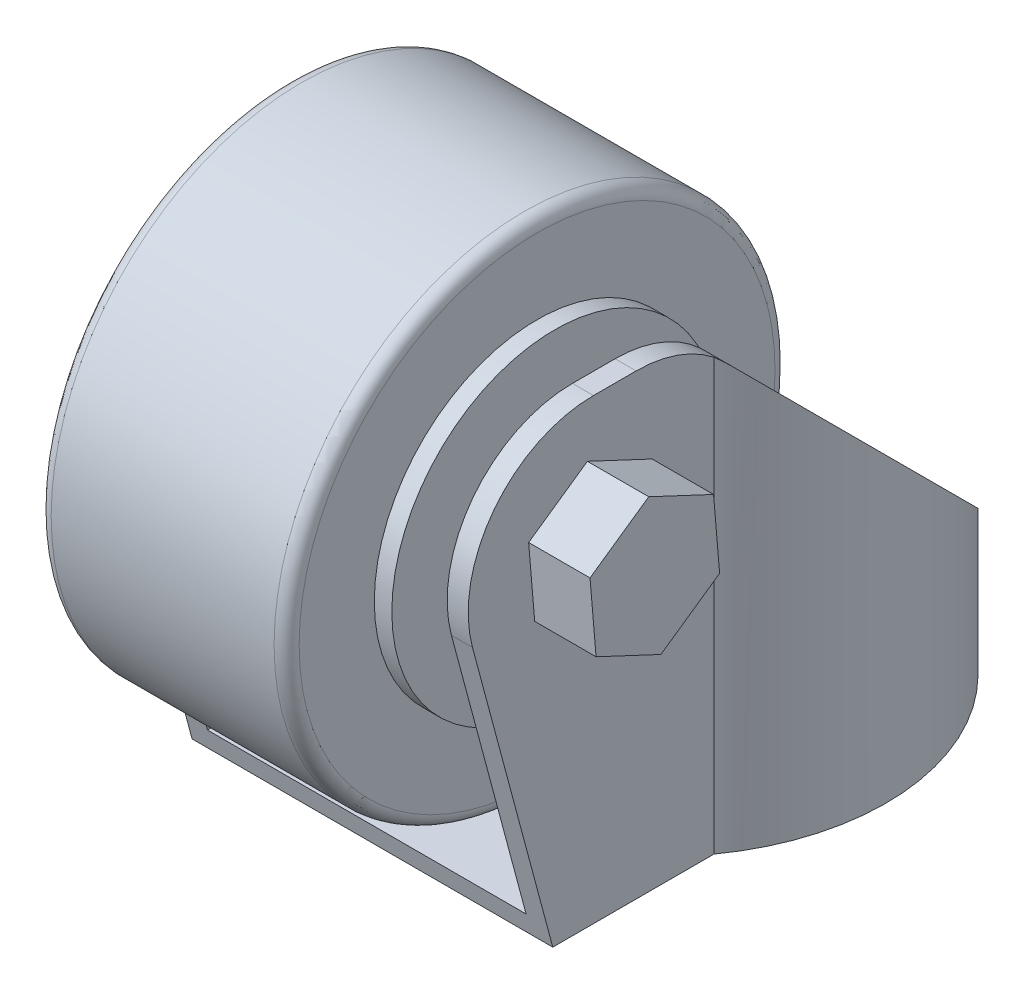
SolidWorks part; units mm, degrees
ref_plane "前视基准面" through (0, 0, 0) normal (0, 0, 1) x (1, 0, 0)
ref_plane "上视基准面" through (0, 0, 0) normal (0, 1, 0) x (1, 0, 0)
ref_plane "右视基准面" through (0, 0, 0) normal (1, 0, 0) x (0, 0, -1)
sketch "草图1" plane through (0, 0, 0) normal (0, 1, 0) x (1, 0, 0)
  line L0 (0, 0) -> (0, 47.6853) construction
  line L1 (-15.1, -30) -> (15.1, -30)
  line L2 (-21.5, -23.6) -> (-21.5, 23.6)
  line L3 (-15.1, 30) -> (15.1, 30)
  line L4 (21.5, -23.6) -> (21.5, 23.6)
  line L5 (-21.5, -30) -> (21.5, 30) construction
  line L6 (-21.5, 30) -> (21.5, -30) construction
  line L7 (0, 0) -> (47.9622, 0) construction
  line L8 (-18.2, 21.05) -> (-18.2, 23.95)
  line L9 (18.2, 23.95) -> (11.8, 21.05) construction
  line L10 (-11.8, 21.05) -> (-11.8, 23.95)
  line L11 (-18.2, 21.05) -> (-11.8, 23.95) construction
  line L12 (-18.2, 23.95) -> (-11.8, 21.05) construction
  line L13 (18.2, 21.05) -> (11.8, 23.95) construction
  line L14 (11.8, 21.05) -> (11.8, 23.95)
  line L15 (18.2, 21.05) -> (18.2, 23.95)
  line L16 (18.2, -21.05) -> (11.8, -23.95) construction
  line L17 (-18.2, -23.95) -> (-11.8, -21.05) construction
  line L18 (-18.2, -21.05) -> (-11.8, -23.95) construction
  line L19 (18.2, -23.95) -> (11.8, -21.05) construction
  line L20 (18.2, -21.05) -> (18.2, -23.95)
  line L21 (11.8, -21.05) -> (11.8, -23.95)
  line L22 (-11.8, -21.05) -> (-11.8, -23.95)
  line L23 (-18.2, -21.05) -> (-18.2, -23.95)
  line L24 (-15.1, -30) -> (15.1, -30)
  arc A0 (-18.2, 23.95) -> (-11.8, 23.95) centre (-15, 23.95) cw
  arc A1 (-18.2, 21.05) -> (-11.8, 21.05) centre (-15, 21.05) ccw
  arc A2 (18.2, 21.05) -> (11.8, 21.05) centre (15, 21.05) cw
  arc A3 (18.2, 23.95) -> (11.8, 23.95) centre (15, 23.95) ccw
  arc A4 (18.2, -23.95) -> (11.8, -23.95) centre (15, -23.95) cw
  arc A5 (18.2, -21.05) -> (11.8, -21.05) centre (15, -21.05) ccw
  arc A6 (-18.2, -21.05) -> (-11.8, -21.05) centre (-15, -21.05) cw
  arc A7 (-18.2, -23.95) -> (-11.8, -23.95) centre (-15, -23.95) ccw
  arc A8 (-21.5, -23.6) -> (-15.1, -30) centre (-15.1, -23.6) ccw
  arc A9 (15.1, -30) -> (21.5, -23.6) centre (15.1, -23.6) ccw
  arc A10 (21.5, 23.6) -> (15.1, 30) centre (15.1, 23.6) ccw
  arc A11 (-21.5, 23.6) -> (-15.1, 30) centre (-15.1, 23.6) cw
  point P0 (0, 0)
  point P6 (-15, 22.5)
  point P22 (15, 22.5)
  point P35 (15, -22.5)
  point P36 (-15, -22.5)
  dimension "D4" = 2.9
  dimension "D7" = 6.4
  dimension "D1" = 43
  dimension "D2" = 60
  dimension "D3" = 6.4
  dimension "D5" = 30
  dimension "D6" = 45
extrude "凸台-拉伸1" add sketch "草图1" along normal blind 1.68 contours A11 L2 A8 L1 A9 L4 A10 L3 A7 L23 A6 L22 A5 L20 A4 L21 A3 L15 A2 L14 A1 L8 A0 L10
sketch "草图2" plane through (0, 1.68, 0) normal (0, 1, 0) x (1, 0, 0)
  circle A0 centre (0, 0) radius 14.75
  dimension "D1" = 29.5
extrude "凸台-拉伸3" add sketch "草图2" along normal blind 5
sketch "草图3" plane through (0, 6.68, 0) normal (0, 1, 0) x (1, 0, 0)
  line L1 (-14.4, -10.378) -> (-14.4, -50)
  line L2 (14.4, -10.378) -> (14.4, -50)
  line L3 (-14.4, -50) -> (14.4, -50)
  arc A0 (14.4, -10.378) -> (-14.4, -10.378) centre (0, 0) ccw
  dimension "D1" = 35.5
  dimension "D2" = 28.8
  dimension "D3" = 50
extrude "凸台-拉伸4" add sketch "草图3" along normal blind 1.68
sketch "草图4" plane through (0, 8.36, 0) normal (0, 1, 0) x (1, 0, 0)
  line L4 (-14.4, -50) -> (-12.72, -50)
  line L5 (12.72, -50) -> (12.72, -9.8207)
  line L6 (-12.72, -9.8207) -> (-12.72, -50)
  line L7 (12.72, -50) -> (12.72, -9.8207)
  line L8 (-12.72, -9.8207) -> (-12.72, -50)
  line L9 (12.72, -50) -> (14.4, -50)
  line L10 (14.4, -50) -> (14.4, -10.378)
  line L11 (-14.4, -10.378) -> (-14.4, -50)
  line L12 (14.4, -50) -> (14.4, -10.378)
  line L13 (-14.4, -10.378) -> (-14.4, -50)
  arc A3 (14.4, -10.378) -> (-14.4, -10.378) centre (0, 0) ccw
  arc A4 (12.72, -9.8207) -> (-12.72, -9.8207) centre (0, 0) ccw
  arc A5 (12.72, -9.8207) -> (-12.72, -9.8207) centre (0, 0) ccw
  arc A6 (14.4, -10.378) -> (-14.4, -10.378) centre (0, 0) ccw
  dimension "D1" = 1.68
  dimension "D2" = 0
extrude "凸台-拉伸5" add sketch "草图4" along normal blind 40
sketch "草图5" plane through (0, 0, 0) normal (1, 0, 0) x (0, 0, -1)
  line L0 (-12.45, 43.2) -> (-33.0355, 43.2)
  line L1 (-23.6, 0) -> (23.6, 0) construction
  line L3 (0, 48.36) -> (0, 6.68) construction
  line L4 (17.75, 6.68) -> (17.75, 48.36) construction
  line L6 (-14.75, 6.68) -> (14.75, 6.68) construction
  line L7 (-33.0355, 43.2) -> (-22.7547, 4.8316)
  line L8 (-12.45, 43.2) -> (24.9674, 5.7826)
  point P6 (0, 30.75)
  point P7 (17.75, 13)
  point P14 (-23.25, 6.68)
  dimension "D1" = 43.2
  dimension "D2" = 45
  dimension "D3" = 13
  dimension "D4" = 75
  dimension "D5" = 41
extrude "切除-拉伸-薄壁1" cut sketch "草图5" against normal mid plane 60 thin
fillet "圆角1" radius 10 4 edges at (-13.56, 43.2, 33.0355) (-13.56, 43.2, 12.45) (13.56, 43.2, 12.45) (13.56, 43.2, 33.0355)
sketch "草图6" plane through (0, 0, 0) normal (1, 0, 0) x (0, 0, -1)
  circle A0 centre (-20.0033, 33.2) radius 20
  point P0 (-20.0033, 33.2)
extrude "凸台-拉伸6" add sketch "草图6" along normal mid plane 19.8 separate body
sketch "草图7" plane through (0, 0, 0) normal (1, 0, 0) x (0, 0, -1)
  circle A0 centre (-20.0033, 33.2) radius 13
extrude "凸台-拉伸7" add sketch "草图7" along normal mid plane 22.6
sketch "草图8" plane through (0, 0, 0) normal (1, 0, 0) x (0, 0, -1)
  line L1 (-24.693, 29.9326) -> (-19.5185, 27.5048)
  line L2 (-19.5185, 27.5048) -> (-14.8287, 30.7722)
  line L3 (-14.8287, 30.7722) -> (-15.3135, 36.4674)
  line L4 (-15.3135, 36.4674) -> (-20.488, 38.8952)
  line L5 (-20.488, 38.8952) -> (-25.1778, 35.6278)
  line L6 (-25.1778, 35.6278) -> (-24.693, 29.9326)
  circle A0 centre (-20.0033, 33.2) radius 5.7158 construction
  point P0 (-20.0033, 33.2)
  dimension "D1" = 9.9
extrude "凸台-拉伸8" add sketch "草图8" along normal mid plane 38.6
fillet "圆角2" radius 1 2 edges at (-9.9, 33.2, 0.0033) (9.9, 33.2, 0.0033)
sketch "草图9" plane through (0, 0, 0) normal (0, -1, 0) x (1, 0, 0)
  line L1 (33.978, -59.0577) -> (-33.978, -59.0577)
  line L2 (33.978, -59.0577) -> (33.978, 59.0577)
  line L3 (33.978, 59.0577) -> (-33.978, 59.0577)
  line L4 (-33.978, -59.0577) -> (-33.978, 59.0577)
  line L5 (33.978, -59.0577) -> (-33.978, 59.0577) construction
  line L6 (33.978, 59.0577) -> (-33.978, -59.0577) construction
  point P1 (0, 0)
extrude "切除-拉伸1" cut sketch "草图9" against normal up to surface (6.68 mm away) up to face at (0, 6.68, 14.75)
